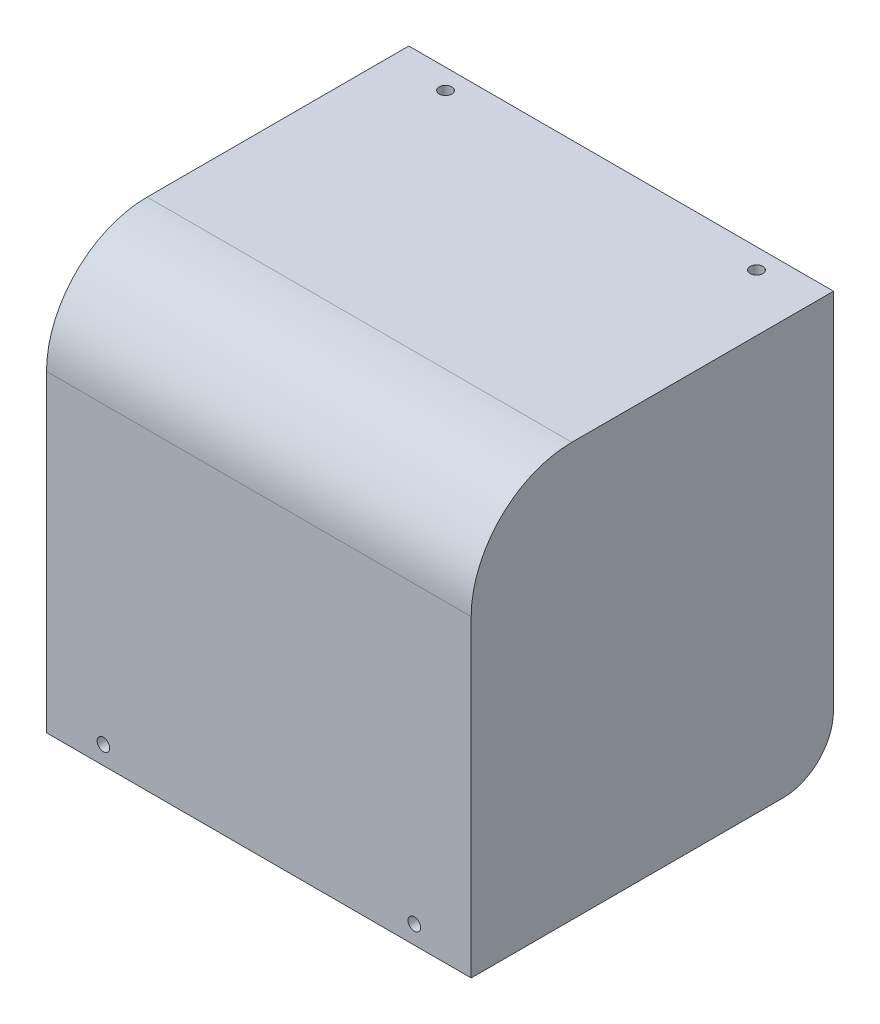
SolidWorks part; units mm, degrees
ref_plane "Front Plane" through (0, 0, 0) normal (0, 0, 1) x (1, 0, 0)
ref_plane "Top Plane" through (0, 0, 0) normal (0, 1, 0) x (1, 0, 0)
ref_plane "Right Plane" through (0, 0, 0) normal (1, 0, 0) x (0, 0, -1)
sketch "Sketch1" plane through (0, 0, 0) normal (1, 0, 0) x (0, 0, -1)
  line L0 (0, 0) -> (0, 82.2)
  line L1 (0, 82.2) -> (72, 82.2)
  line L2 (72, 82.2) -> (72, 80.2)
  line L3 (72, 80.2) -> (2, 80.2)
  line L4 (2, 80.2) -> (2, 0)
  line L5 (2, 0) -> (0, 0)
  dimension "D1" = 80.2
  dimension "D2" = 70
  dimension "D3" = 2
  dimension "D4" = 2
extrude "Boss-Extrude1" add sketch "Sketch1" along normal mid plane 84.4
sketch "Sketch2" plane through (0, 0, 0) normal (0, 0, 1) x (1, 0, 0)
  line L0 (-42.2, 3.64) -> (42.2, 3.64) construction
  line L1 (-42.2, 82.2) -> (-42.2, 0) construction
  line L2 (42.2, 82.2) -> (42.2, 0) construction
  line L3 (0, 3.64) -> (0, 0) construction
  line L4 (42.2, 0) -> (-42.2, 0) construction
  circle A0 centre (-30.9, 3.64) radius 1.25
  circle A1 centre (30.9, 3.64) radius 1.25
  dimension "D2" = 2.5
  dimension "D1" = 61.8
  dimension "D3" = 3.64
extrude "Cut-Extrude1" cut sketch "Sketch2" against normal blind 70
fillet "Fillet1" radius 20 2 edges at (0, 82.2, 0) (0, 80.2, -2)
sketch "Sketch3" plane through (-42.2, 0, 0) normal (-1, 0, 0) x (0, 0, 1)
  line L0 (-72, 80.2) -> (-72, 0)
  line L1 (-72, 0) -> (-2, 0)
  line L2 (-2, 0) -> (-2, 60.2) construction
  line L3 (-22, 80.2) -> (-72, 80.2) construction
  line L4 (-2, 0) -> (-2, 60.2)
  line L5 (-22, 80.2) -> (-72, 80.2)
  arc A0 (-2, 60.2) -> (-22, 80.2) centre (-22, 60.2) ccw construction
  arc A1 (-2, 60.2) -> (-22, 80.2) centre (-22, 60.2) ccw
extrude "Boss-Extrude2" add sketch "Sketch3" against normal blind 2
mirror "Mirror1" about plane through (0, 0, 0) normal (1, 0, 0) of "Boss-Extrude2"
fillet "Fillet2" radius 10 2 edges at (-41.2, 0, -72) (41.2, 0, -72)
sketch "Sketch4" plane through (0, 82.2, 0) normal (0, 1, 0) x (1, 0, 0)
  line L0 (-42.2, 68.002) -> (42.2, 68.002) construction
  line L1 (0, 68.002) -> (0, 72) construction
  line L2 (42.2, 72) -> (42.2, 20) construction
  line L3 (-42.2, 72) -> (-42.2, 20) construction
  line L4 (42.2, 72) -> (-42.2, 72) construction
  circle A0 centre (-30.9, 68.002) radius 1.25
  circle A1 centre (30.9, 68.002) radius 1.25
  dimension "D1" = 2.5
  dimension "D2" = 61.8
  dimension "D3" = 3.998
extrude "Cut-Extrude2" cut sketch "Sketch4" against normal blind 10
